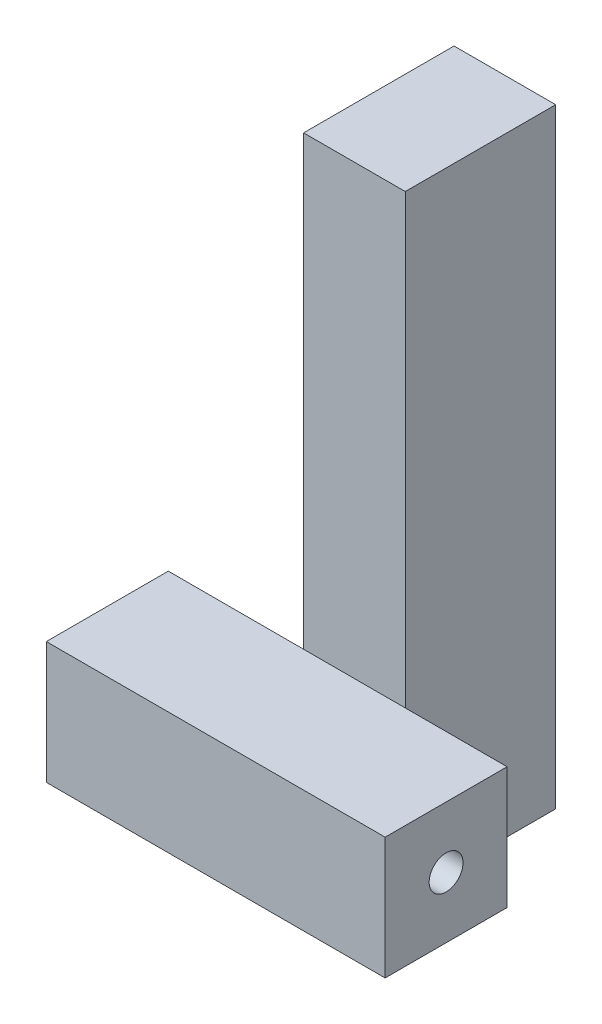
SolidWorks part; units mm, degrees
ref_plane "Front Plane" through (0, 0, 0) normal (0, 0, 1) x (1, 0, 0)
ref_plane "Top Plane" through (0, 0, 0) normal (0, 1, 0) x (1, 0, 0)
ref_plane "Right Plane" through (0, 0, 0) normal (1, 0, 0) x (0, 0, -1)
sketch "Sketch1" plane through (0, 0, 0) normal (0, 0, 1) x (1, 0, 0)
  line L1 (-63.5, 22.86) -> (63.5, 22.86)
  line L2 (-63.5, 22.86) -> (-63.5, -22.86)
  line L3 (-63.5, -22.86) -> (63.5, -22.86)
  line L4 (63.5, 22.86) -> (63.5, -22.86)
  line L5 (-63.5, 22.86) -> (63.5, -22.86) construction
  line L6 (-63.5, -22.86) -> (63.5, 22.86) construction
  point P0 (0, 0)
  dimension "D1" = 45.72
  dimension "D2" = 127
extrude "Boss-Extrude1" add sketch "Sketch1" along normal blind 45.72
sketch "Sketch2" plane through (0, 0, 0) normal (0, 0, -1) x (-1, 0, 0)
  line L0 (63.5, -22.86) -> (-63.5, -22.86) construction
  line L1 (12.7738, -38.1) -> (-25.3262, -38.1)
  line L2 (12.7738, -38.1) -> (12.7738, 190.5)
  line L3 (12.7738, 190.5) -> (-25.3262, 190.5)
  line L4 (-25.3262, -38.1) -> (-25.3262, 190.5)
  dimension "D1" = 15.24
  dimension "D2" = 38.1
  dimension "D3" = 228.6
extrude "Boss-Extrude2" add sketch "Sketch2" along normal blind 56.388
sketch "Sketch3" plane through (63.5, 0, 0) normal (1, 0, 0) x (0, 0, -1)
  line L0 (-22.86, 22.86) -> (-22.86, 0) construction
  line L1 (-45.72, 22.86) -> (0, 22.86) construction
  line L2 (0, 0) -> (-22.86, 0) construction
  circle A0 centre (-22.86, 0) radius 6.35
  dimension "D1" = 12.7
extrude "Cut-Extrude1" cut sketch "Sketch3" against normal blind 15.24
sketch "Sketch4" plane through (-63.5, 0, 0) normal (-1, 0, 0) x (0, 0, 1)
  line L0 (22.86, 22.86) -> (22.86, 0) construction
  line L1 (45.72, 22.86) -> (0, 22.86) construction
  line L2 (0, 0) -> (22.86, 0) construction
  line L3 (0, 22.86) -> (0, -22.86) construction
  circle A0 centre (22.86, 0) radius 6.35
  dimension "D1" = 12.7
extrude "Cut-Extrude2" cut sketch "Sketch4" against normal blind 15.24
